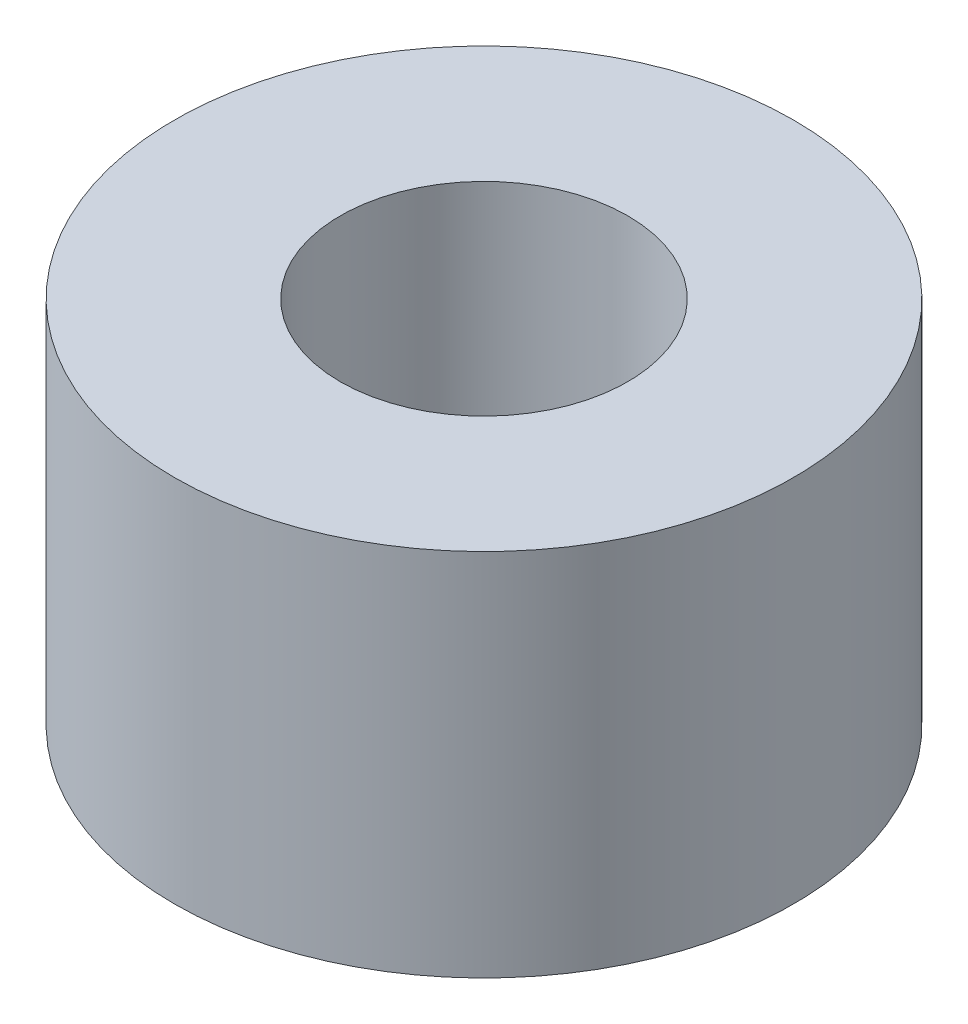
SolidWorks part; units mm, degrees
ref_plane "Front Plane" through (0, 0, 0) normal (0, 0, 1) x (1, 0, 0)
ref_plane "Top Plane" through (0, 0, 0) normal (0, 1, 0) x (1, 0, 0)
ref_plane "Right Plane" through (0, 0, 0) normal (1, 0, 0) x (0, 0, -1)
sketch "Sketch1" plane through (0, 0, 0) normal (0, 1, 0) x (1, 0, 0)
  circle A0 centre (0, 0) radius 3.5
  circle A1 centre (0, 0) radius 1.625
  dimension "D1" = 3.25
  dimension "D2" = 7
extrude "Boss-Extrude1" add sketch "Sketch1" along normal mid plane 4.175
